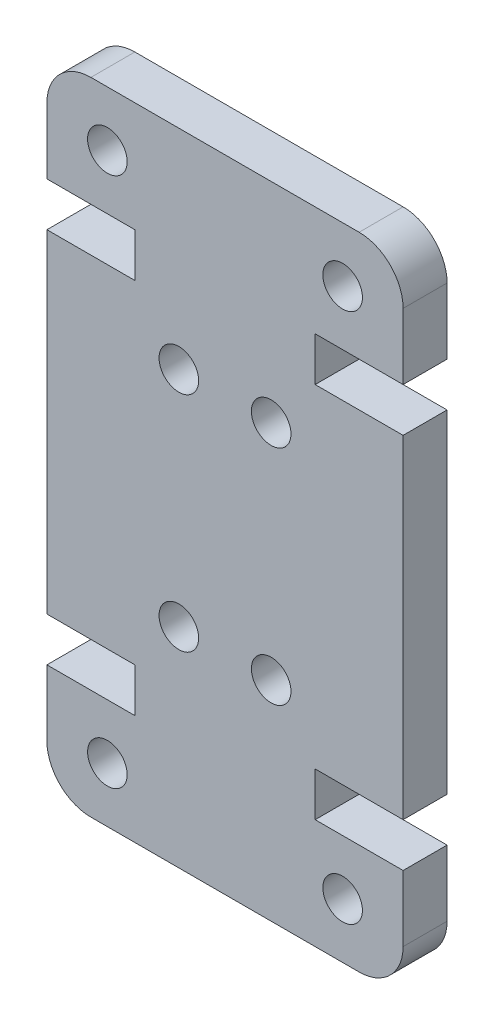
SolidWorks part; units mm, degrees
ref_plane "Front Plane" through (0, 0, 0) normal (0, 0, 1) x (1, 0, 0)
ref_plane "Top Plane" through (0, 0, 0) normal (0, 1, 0) x (1, 0, 0)
ref_plane "Right Plane" through (0, 0, 0) normal (1, 0, 0) x (0, 0, -1)
sketch "Sketch1" plane through (0, 0, 0) normal (0, 0, 1) x (1, 0, 0)
  line L0 (0, 22.14) -> (0, 7)
  line L1 (16.2, 2) -> (16.2, 5)
  line L2 (12.2, 5) -> (16.2, 5)
  line L3 (2, 0) -> (14.2, 0)
  line L4 (16.2, 7) -> (12.2, 7)
  line L5 (12.2, 7) -> (12.2, 5)
  line L6 (16.2, 22.14) -> (16.2, 7)
  line L7 (4, 7) -> (4, 5)
  line L8 (0, 27.14) -> (0, 24.14)
  line L9 (4, 24.14) -> (0, 24.14)
  line L10 (0, 7) -> (4, 7)
  line L11 (0, 22.14) -> (4, 22.14)
  line L12 (4, 5) -> (0, 5)
  line L13 (4, 22.14) -> (4, 24.14)
  line L14 (12.2, 22.14) -> (12.2, 24.14)
  line L15 (16.2, 22.14) -> (12.2, 22.14)
  line L16 (0, 2) -> (0, 5)
  line L17 (2, 29.14) -> (14.2, 29.14)
  line L18 (12.2, 24.14) -> (16.2, 24.14)
  line L19 (16.2, 27.14) -> (16.2, 24.14)
  line L20 (8.1, 29.14) -> (8.1, 0) construction
  line L21 (0, 14.57) -> (16.2, 14.57) construction
  circle A0 centre (13.45, 2.5) radius 0.9
  circle A1 centre (10.2, 9.5) radius 0.9
  arc A2 (16.2, 2) -> (14.2, 0) centre (14.2, 2) cw
  circle A3 centre (2.75, 26.64) radius 0.9
  circle A4 centre (6, 19.64) radius 0.9
  arc A5 (0, 2) -> (2, 0) centre (2, 2) ccw
  arc A6 (0, 27.14) -> (2, 29.14) centre (2, 27.14) cw
  circle A7 centre (6, 9.5) radius 0.9
  arc A8 (16.2, 27.14) -> (14.2, 29.14) centre (14.2, 27.14) ccw
  circle A9 centre (2.75, 2.5) radius 0.9
  circle A10 centre (10.2, 19.64) radius 0.9
  circle A11 centre (13.45, 26.64) radius 0.9
  point P15 (8.1, 14.57)
  dimension "D1" = 1.8
  dimension "D2" = 2
  dimension "D3" = 2.75
  dimension "D4" = 6
  dimension "D5" = 8.1
  dimension "D6" = 2.5
  dimension "D7" = 5
  dimension "D9" = 9.5
  dimension "D10" = 14.57
extrude "Boss-Extrude1" add sketch "Sketch1" along normal blind 2
equation "\"D5@Sketch1\"= \"fingerWidth@parametersSketch@prostheticParameters.SLDPRT\" / 2'PIP width"
equation "\"D10@Sketch1\"= ( \"HL@parametersSketch@prostheticParameters.SLDPRT\" * 0.244 - 4 - 12 ) / 2 'PIP length - Sil.Sht PIP - Sil. Sht MIP"
equation "\"D1@Sketch1\"= 1.5 + \"tol1@parametersSketch@prostheticParameters.SLDPRT\""
